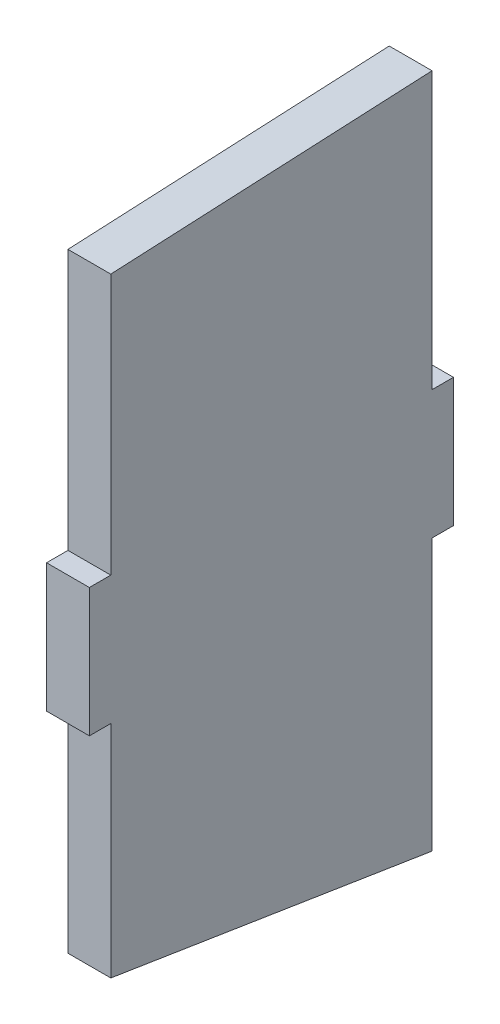
SolidWorks part; units mm, degrees
material "Pink Foam"
ref_plane "Front Plane" through (0, 0, 0) normal (0, 0, 1) x (1, 0, 0)
ref_plane "Top Plane" through (0, 0, 0) normal (0, 1, 0) x (1, 0, 0)
ref_plane "Right Plane" through (0, 0, 0) normal (1, 0, 0) x (0, 0, -1)
sketch "Sketch1" plane through (0, 0, 0) normal (1, 0, 0) x (0, 0, -1)
  line L0 (-95.25, 192.6958) -> (95.25, 201.8798)
  line L1 (-95.25, -203.2) -> (95.25, -203.2)
  line L2 (-95.25, -203.2) -> (-95.25, 203.2)
  line L3 (-95.25, 203.2) -> (95.25, 203.2)
  line L4 (95.25, -203.2) -> (95.25, 203.2)
  line L5 (-95.25, -203.2) -> (95.25, 203.2) construction
  line L6 (-95.25, 203.2) -> (95.25, -203.2) construction
  line L7 (-107.95, -38.1) -> (107.95, -38.1)
  line L8 (-107.95, -38.1) -> (-107.95, 38.1)
  line L9 (-107.95, 38.1) -> (107.95, 38.1)
  line L10 (107.95, -38.1) -> (107.95, 38.1)
  line L11 (-107.95, -38.1) -> (107.95, 38.1) construction
  line L12 (-107.95, 38.1) -> (107.95, -38.1) construction
  line L14 (-95.25, -168.8002) -> (95.25, -198.8953)
  point P0 (0, 0)
  point P6 (0, 0)
  dimension "D1" = 190.5
  dimension "D2" = 215.9
  dimension "D3" = 76.2
  dimension "D4" = 406.4
  dimension "D5" = 10.5042
  dimension "D6" = 1.3202
  dimension "D7" = 4.3047
  dimension "D8" = 361.496
extrude "Boss-Extrude1" add sketch "Sketch1" along normal blind 25.4 contours L2 L9 L4 L0 | L7 L10 L9 L4 | L9 L2 L7 L4 | L9 L8 L7 L2 | L2 L14 L4 L7
